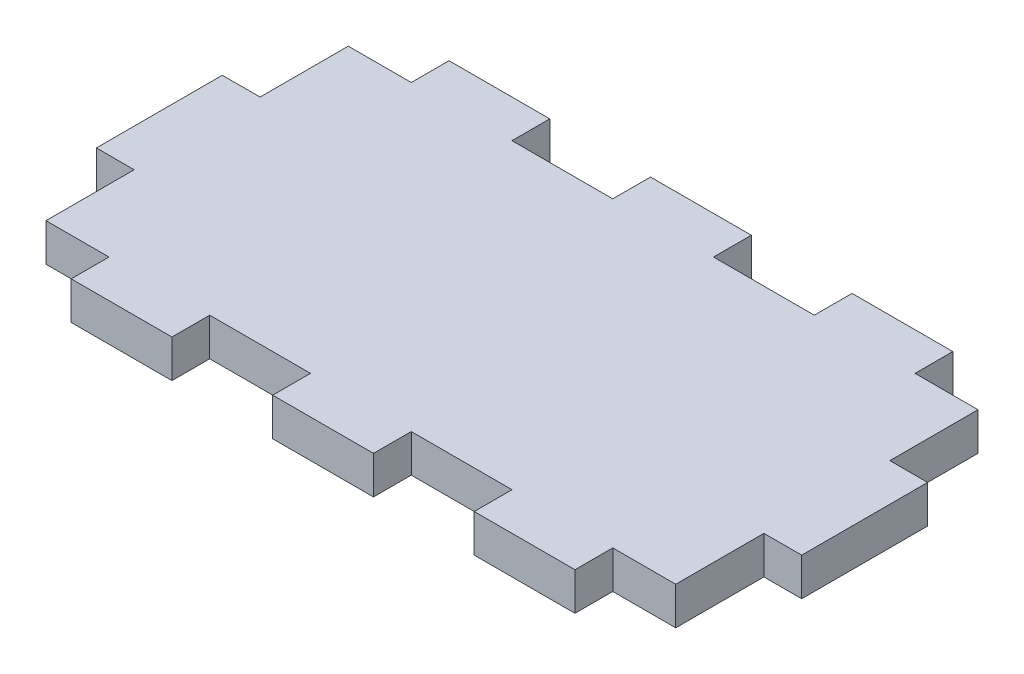
SolidWorks part; units mm, degrees
ref_plane "Front" through (0, 0, 0) normal (0, 0, 1) x (1, 0, 0)
ref_plane "Top" through (0, 0, 0) normal (0, 1, 0) x (1, 0, 0)
ref_plane "Right" through (0, 0, 0) normal (1, 0, 0) x (0, 0, -1)
sketch "Skizze1" plane through (0, 0, 0) normal (0, 1, 0) x (1, 0, 0)
  line L1 (0, 0) -> (56, 0) construction
  line L2 (0, 0) -> (0, 30) construction
  line L3 (0, 30) -> (56, 30) construction
  line L4 (56, 0) -> (56, 30) construction
  line L140 (3, 26.9999) -> (3, 19.9997)
  line L141 (3, 19.9997) -> (0, 19.9997)
  line L142 (0, 19.9997) -> (0, 10.0007)
  line L143 (3, 10.0007) -> (0, 10.0007)
  line L144 (3, 10.0007) -> (3, 3.0002)
  line L145 (53.0007, 26.9999) -> (53.0007, 19.9997)
  line L146 (56.0007, 19.9997) -> (53.0007, 19.9997)
  line L147 (56.0007, 19.9997) -> (56.0007, 10.0007)
  line L148 (56.0007, 10.0007) -> (53.0007, 10.0007)
  line L149 (53.0007, 10.0007) -> (53.0007, 3.0002)
  line L150 (3, 26.9999) -> (8.001, 26.9999)
  line L151 (8.001, 26.9999) -> (8.001, 29.9999)
  line L152 (8.001, 29.9999) -> (16.0002, 29.9999)
  line L153 (16.0002, 26.9999) -> (16.0002, 29.9999)
  line L154 (16.0002, 26.9999) -> (24, 26.9999)
  line L155 (24, 26.9999) -> (24, 29.9999)
  line L156 (24, 29.9999) -> (32.001, 29.9999)
  line L157 (32.001, 26.9999) -> (32.001, 29.9999)
  line L158 (32.001, 26.9999) -> (40.0004, 26.9999)
  line L159 (40.0004, 26.9999) -> (40.0004, 29.9999)
  line L160 (40.0004, 29.9999) -> (48.0012, 29.9999)
  line L161 (48.0012, 26.9999) -> (48.0012, 29.9999)
  line L162 (48.0012, 26.9999) -> (53.0007, 26.9999)
  line L163 (3, 3.0002) -> (8.001, 3.0002)
  line L164 (8.001, 0) -> (8.001, 3.0002)
  line L165 (8.001, 0) -> (16.0002, 0)
  line L166 (16.0002, 0) -> (16.0002, 3.0002)
  line L167 (16.0002, 3.0002) -> (24, 3.0002)
  line L168 (24, 0) -> (24, 3.0002)
  line L169 (24, 0) -> (32.001, 0)
  line L170 (32.001, 0) -> (32.001, 3.0002)
  line L171 (32.001, 3.0002) -> (40.0004, 3.0002)
  line L172 (40.0004, 0) -> (40.0004, 3.0002)
  line L173 (40.0004, 0) -> (48.0012, 0)
  line L174 (48.0012, 0) -> (48.0012, 3.0002)
  line L175 (48.0012, 3.0002) -> (53.0007, 3.0002)
  dimension "D1" = 56
  dimension "D2" = 30
extrude "Aufsatz-Linear austragen1" add sketch "Skizze1" along normal blind 3
equation "\"D4@Skizze4\"=\"D1@Skizze4\""
